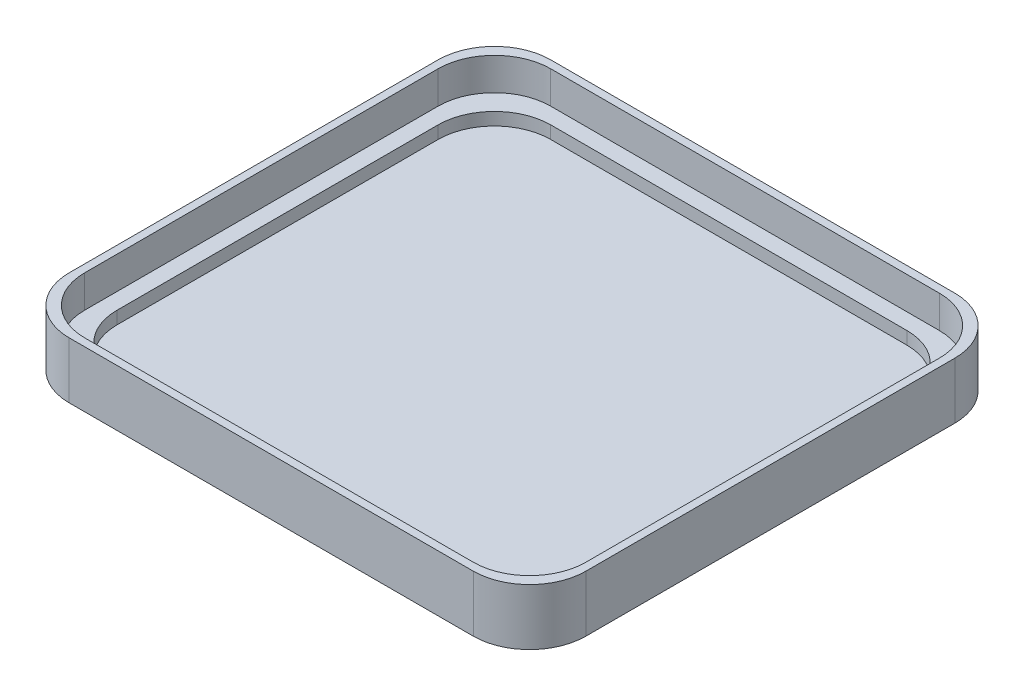
SolidWorks part; units mm, degrees
ref_plane "Front Plane" through (0, 0, 0) normal (0, 0, 1) x (1, 0, 0)
ref_plane "Top Plane" through (0, 0, 0) normal (0, 1, 0) x (1, 0, 0)
ref_plane "Right Plane" through (0, 0, 0) normal (1, 0, 0) x (0, 0, -1)
sketch "Sketch1" plane through (0, 0, 0) normal (0, 1, 0) x (1, 0, 0)
  line L1 (-46.609, -43.434) -> (46.609, -43.434)
  line L2 (-46.609, -43.434) -> (-46.609, 43.434)
  line L3 (-46.609, 43.434) -> (46.609, 43.434)
  line L4 (46.609, -43.434) -> (46.609, 43.434)
  line L5 (-46.609, -43.434) -> (46.609, 43.434) construction
  line L6 (-46.609, 43.434) -> (46.609, -43.434) construction
  point P0 (0, 0)
extrude "Boss-Extrude1" add sketch "Sketch1" along normal blind 10.16
sketch "Sketch2" plane through (0, 10.16, 0) normal (0, 1, 0) x (1, 0, 0)
  line L1 (-45.212, -42.037) -> (45.212, -42.037)
  line L2 (-45.212, -42.037) -> (-45.212, 42.037)
  line L3 (-45.212, 42.037) -> (45.212, 42.037)
  line L4 (45.212, -42.037) -> (45.212, 42.037)
  line L5 (-45.212, -42.037) -> (45.212, 42.037) construction
  line L6 (-45.212, 42.037) -> (45.212, -42.037) construction
  point P0 (0, 0)
extrude "Cut-Extrude1" cut sketch "Sketch2" against normal blind 5.842
sketch "Sketch3" plane through (0, 4.318, 0) normal (0, 1, 0) x (1, 0, 0)
  line L1 (-42.291, -39.116) -> (42.291, -39.116)
  line L2 (-42.291, -39.116) -> (-42.291, 39.116)
  line L3 (-42.291, 39.116) -> (42.291, 39.116)
  line L4 (42.291, -39.116) -> (42.291, 39.116)
  line L5 (-42.291, -39.116) -> (42.291, 39.116) construction
  line L6 (-42.291, 39.116) -> (42.291, -39.116) construction
  point P0 (0, 0)
extrude "Cut-Extrude2" cut sketch "Sketch3" against normal blind 2.286
fillet "Fillet1" radius 10.16 12 edges at (-45.212, 7.239, 42.037) (-42.291, 3.175, 39.116) (-46.609, 5.08, 43.434) (42.291, 3.175, 39.116) (45.212, 7.239, 42.037) (46.609, 5.08, 43.434) (46.609, 5.08, -43.434) (45.212, 7.239, -42.037) (42.291, 3.175, -39.116) (-46.609, 5.08, -43.434) (-45.212, 7.239, -42.037) (-42.291, 3.175, -39.116)
